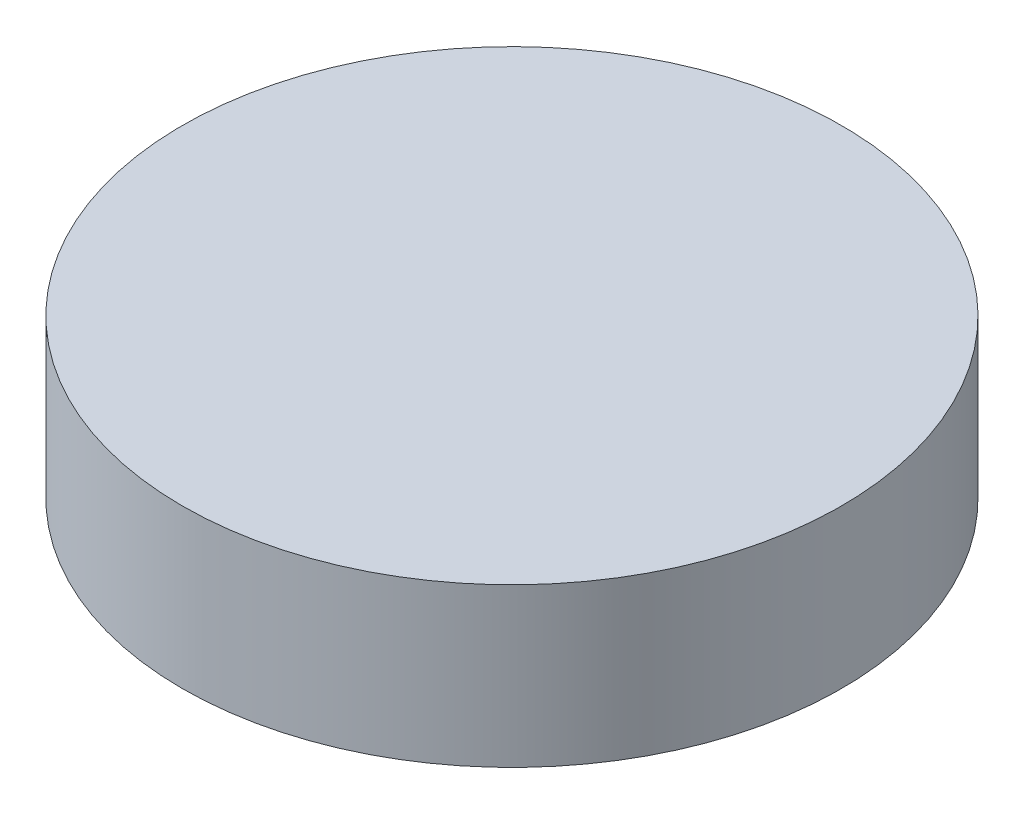
SolidWorks part; units mm, degrees
ref_plane "Front" through (0, 0, 0) normal (0, 0, 1) x (1, 0, 0)
ref_plane "Top" through (0, 0, 0) normal (0, 1, 0) x (1, 0, 0)
ref_plane "Right" through (0, 0, 0) normal (1, 0, 0) x (0, 0, -1)
sketch "Sketch2" plane through (0, 0, 0) normal (0, 1, 0) x (1, 0, 0)
  circle A0 centre (0, 0) radius 12.5
  dimension "D1" = 25
extrude "Boss-Extrude1" add sketch "Sketch2" along normal mid plane 6
sketch "Sketch4" plane through (0, -3, 0) normal (0, -1, 0) x (-1, 0, 0)
  circle A0 centre (0, 0) radius 3
  dimension "D1" = 6
extrude "Cut-Extrude2" cut sketch "Sketch4" against normal blind 3
